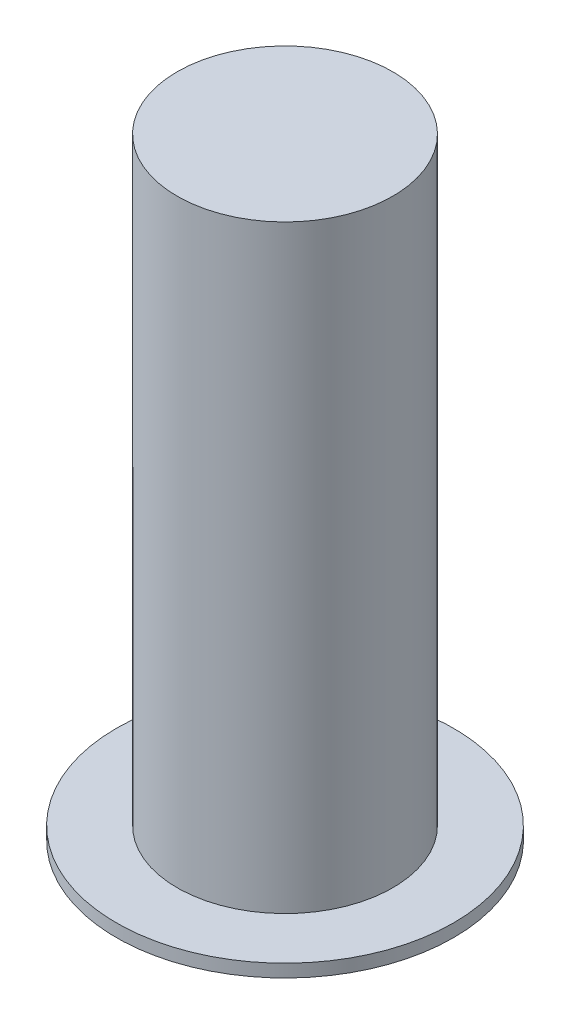
SolidWorks part; units mm, degrees
ref_plane "Front Plane" through (0, 0, 0) normal (0, 0, 1) x (1, 0, 0)
ref_plane "Top Plane" through (0, 0, 0) normal (0, 1, 0) x (1, 0, 0)
ref_plane "Right Plane" through (0, 0, 0) normal (1, 0, 0) x (0, 0, -1)
sketch "Sketch1" plane through (0, 0, 0) normal (0, 0, 1) x (1, 0, 0)
  line L0 (-8.545, 0) -> (-5.465, 0)
  line L1 (-5.465, 0) -> (-5.465, 30.36)
  line L2 (-5.465, 30.36) -> (0, 30.36)
  line L3 (0, 30.36) -> (0, 16.55)
  line L4 (0, 16.55) -> (-5.135, 16.55)
  line L5 (-5.135, 16.55) -> (-5.135, -0.65)
  line L6 (-5.135, -0.65) -> (-8.545, -0.65)
  line L7 (-8.545, -0.65) -> (-8.545, 0)
  dimension "D1" = 0.65
  dimension "D2" = 8.545
  dimension "D3" = 3.41
  dimension "D4" = 31.01
  dimension "D5" = 17.2
  dimension "D6" = 5.465
revolve "Revolve1" add sketch "Sketch1" angle 360 about L3
